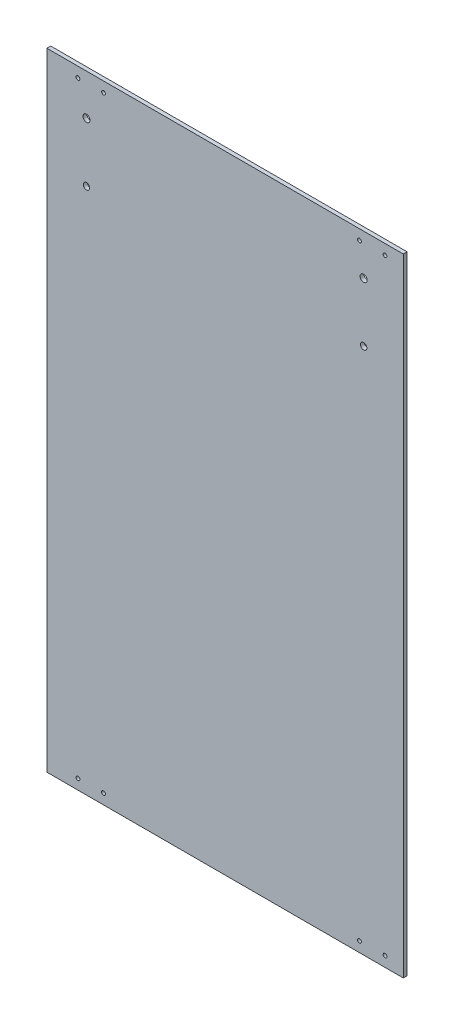
SolidWorks part; units mm, degrees
ref_plane "前视基准面" through (0, 0, 0) normal (0, 0, 1) x (1, 0, 0)
ref_plane "上视基准面" through (0, 0, 0) normal (0, 1, 0) x (1, 0, 0)
ref_plane "右视基准面" through (0, 0, 0) normal (1, 0, 0) x (0, 0, -1)
other "Configuration Table"
sketch "草图1" plane through (0, 0, 0) normal (0, 0, 1) x (1, 0, 0)
  line L1 (-139.28, 245) -> (139.28, 245)
  line L2 (-139.28, 245) -> (-139.28, -245)
  line L3 (-139.28, -245) -> (139.28, -245)
  line L4 (139.28, 245) -> (139.28, -245)
  line L5 (-139.28, 245) -> (139.28, -245) construction
  line L6 (-139.28, -245) -> (139.28, 245) construction
  line L9 (245.0535, 242) -> (105.7719, 242) construction
  line L13 (88.4514, 242) -> (105.7719, 242) construction
  circle A0 centre (104.9991, 237) radius 1.5
  circle A1 centre (124.9991, 237) radius 1.5
  circle A2 centre (-95.0009, 237) radius 1.5
  circle A3 centre (-115.0009, 237) radius 1.5
  circle A4 centre (124.9991, -237) radius 1.5
  circle A5 centre (104.9991, -237) radius 1.5
  circle A6 centre (-95.0009, -237) radius 1.5
  circle A7 centre (-115.0009, -237) radius 1.5
  point P0 (0, 0)
  dimension "D3" = 24.2791
  dimension "D4" = 20
  dimension "D9" = 14.2809
  dimension "D1" = 490
  dimension "D2" = 278.56
  dimension "D8" = 20
  dimension "D11" = 24.2791
  dimension "D14" = 20
  dimension "D15" = 20
  dimension "D16" = 14.2809
  dimension "D17" = 5
  dimension "D18" = 5
extrude "凸台-拉伸1" add sketch "草图1" along normal blind 3
sketch "草图2" plane through (0, 0, 0) normal (0, 0, -1) x (-1, 0, 0)
  circle A0 centre (-108.2752, 167.0881) radius 2.5
  circle A1 centre (108.2848, 167.0881) radius 2.5
  dimension "D1" = 5
  dimension "D2" = 5
extrude "切除-拉伸1" cut sketch "草图2" against normal blind 10
sketch "草图3" plane through (0, 0, 0) normal (0, 0, -1) x (-1, 0, 0)
  circle A0 centre (108.2848, 213.0881) radius 2.75 construction
  circle A1 centre (108.2848, 213.0881) radius 2.75
  circle A2 centre (-108.2752, 213.0881) radius 2.75 construction
  circle A3 centre (-108.2752, 213.0881) radius 2.75
extrude "切除-拉伸2" cut sketch "草图3" against normal through all both and the other way through all
